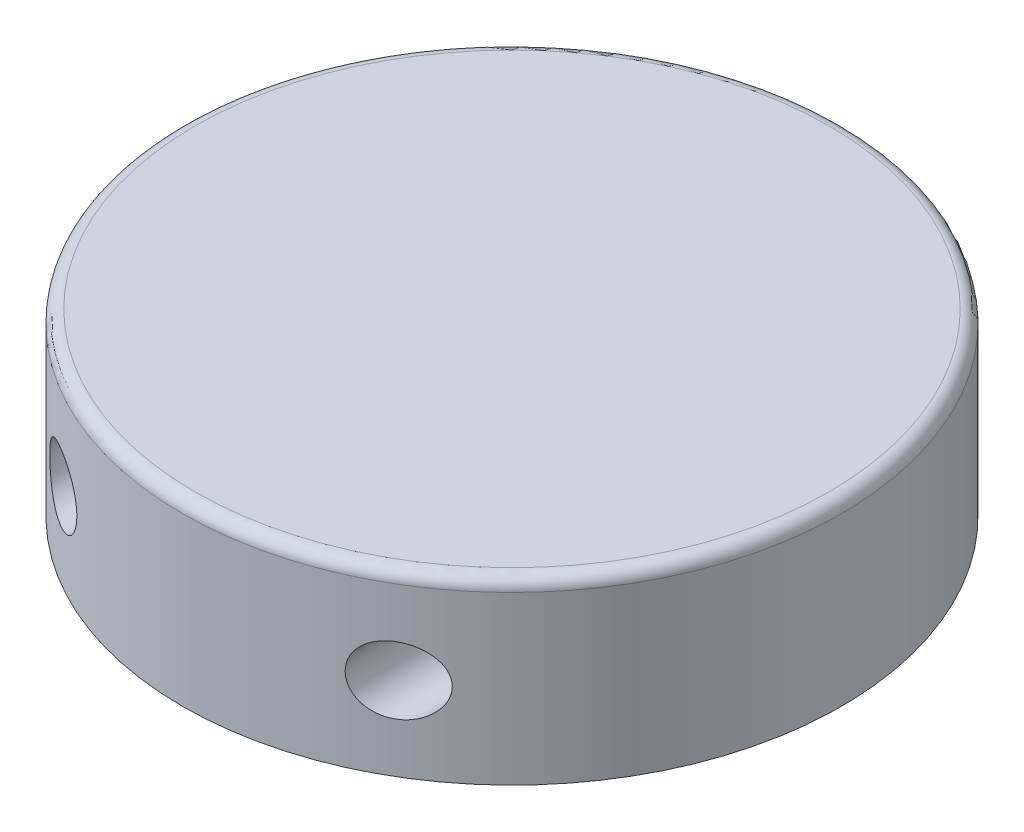
SolidWorks part; units mm, degrees
ref_plane "Front Plane" through (0, 0, 0) normal (0, 0, 1) x (1, 0, 0)
ref_plane "Top Plane" through (0, 0, 0) normal (0, 1, 0) x (1, 0, 0)
ref_plane "Right Plane" through (0, 0, 0) normal (1, 0, 0) x (0, 0, -1)
sketch "Sketch1" plane through (0, 0, 0) normal (0, 1, 0) x (1, 0, 0)
  circle A0 centre (0, 0) radius 39.3
  dimension "D1" = 78.6
extrude "Boss-Extrude1" add sketch "Sketch1" along normal blind 21.4
fillet "Fillet1" radius 1.5 1 edges at (0, 21.4, 39.3)
ref_plane "Plane1" through (0, 0, 39.3) normal (0, 0, 1) x (1, 0, 0)
sketch "Sketch2" plane through (0, 0, 39.3) normal (0, 0, 1) x (1, 0, 0)
  line L0 (-39.3, 9.95) -> (39.3, 9.95) construction
  line L1 (-39.3, 19.9) -> (-39.3, 0) construction
  line L2 (39.3, 0) -> (39.3, 19.9) construction
  line L3 (0, 21.4) -> (0, 0) construction
  line L4 (37.8, 21.4) -> (-37.8, 21.4) construction
  circle A0 centre (-20, 9.95) radius 4
  circle A1 centre (20, 9.95) radius 4
  dimension "D1" = 8
  dimension "D2" = 40
extrude "Cut-Extrude1" cut sketch "Sketch2" against normal blind 50
